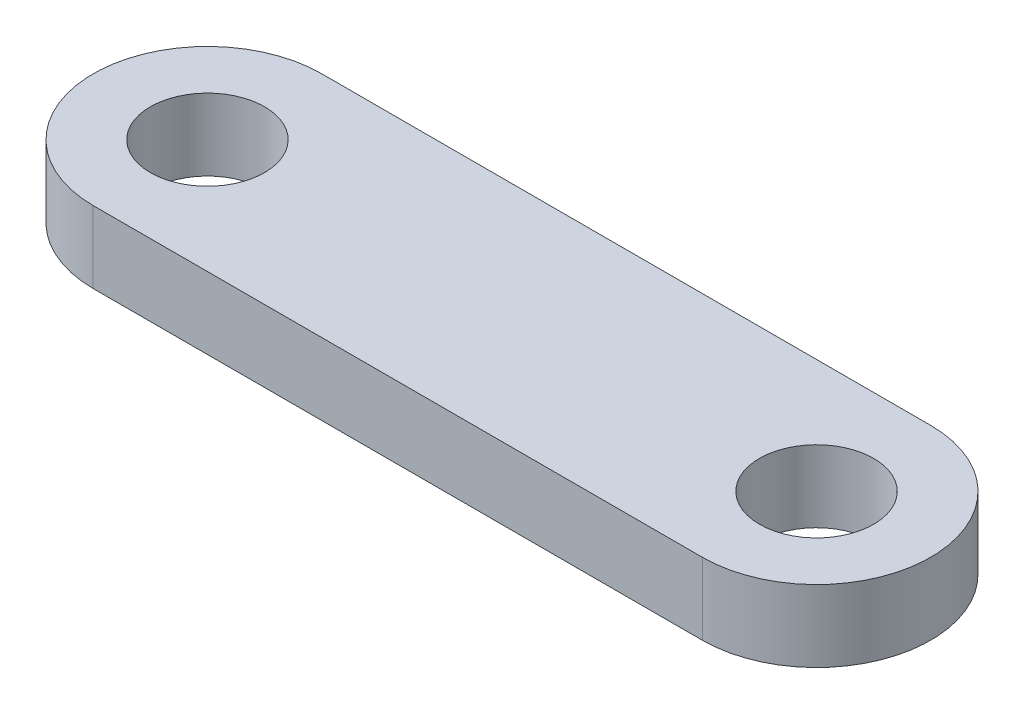
SolidWorks part; units mm, degrees
ref_plane "Front Plane" through (0, 0, 0) normal (0, 0, 1) x (1, 0, 0)
ref_plane "Top Plane" through (0, 0, 0) normal (0, 1, 0) x (1, 0, 0)
ref_plane "Right Plane" through (0, 0, 0) normal (1, 0, 0) x (0, 0, -1)
sketch "Sketch1" plane through (0, 0, 0) normal (0, 1, 0) x (1, 0, 0)
  line L0 (-12.7, 0) -> (12.7, 0) construction
  line L1 (-12.7, 4.7625) -> (12.7, 4.7625)
  line L2 (-12.7, -4.7625) -> (12.7, -4.7625)
  arc A0 (-12.7, 4.7625) -> (-12.7, -4.7625) centre (-12.7, 0) ccw
  arc A1 (12.7, -4.7625) -> (12.7, 4.7625) centre (12.7, 0) ccw
  circle A2 centre (-12.7, 0) radius 2.3813
  circle A3 centre (12.7, 0) radius 2.3813
  point P2 (0, 0)
  dimension "D3" = 4.7625
  dimension "D1" = 25.4
  dimension "D2" = 9.525
extrude "Extrude1" add sketch "Sketch1" along normal mid plane 2.9972
